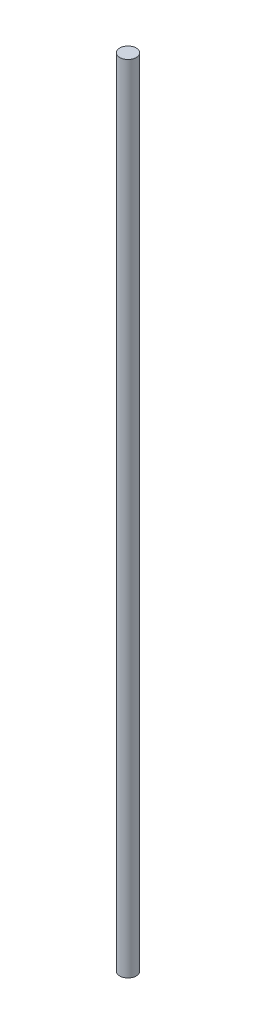
SolidWorks part; units mm, degrees
material "Chrome Stainless Steel"
ref_plane "Front Plane" through (0, 0, 0) normal (0, 0, 1) x (1, 0, 0)
ref_plane "Top Plane" through (0, 0, 0) normal (0, 1, 0) x (1, 0, 0)
ref_plane "Right Plane" through (0, 0, 0) normal (1, 0, 0) x (0, 0, -1)
sketch "Sketch1" plane through (0, 0, 0) normal (0, 1, 0) x (1, 0, 0)
  circle A0 centre (0, 0) radius 4
  dimension "D1" = 8
extrude "Boss-Extrude1" add sketch "Sketch1" along normal blind 385
